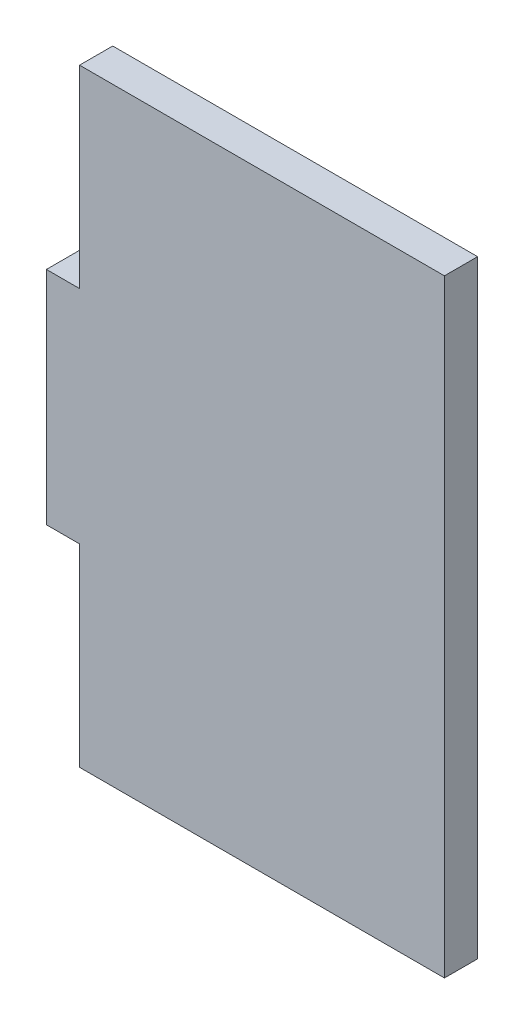
SolidWorks part; units mm, degrees
ref_plane "Alzado" through (0, 0, 0) normal (0, 0, 1) x (1, 0, 0)
ref_plane "Planta" through (0, 0, 0) normal (0, 1, 0) x (1, 0, 0)
ref_plane "Vista lateral" through (0, 0, 0) normal (1, 0, 0) x (0, 0, -1)
sketch "Croquis1" plane through (0, 0, 0) normal (0, 0, 1) x (1, 0, 0)
  line L1 (-16.5, 27.5) -> (16.5, 27.5)
  line L2 (-16.5, 27.5) -> (-16.5, -27.5)
  line L3 (-16.5, -27.5) -> (16.5, -27.5)
  line L4 (16.5, 27.5) -> (16.5, -27.5)
  line L5 (-16.5, 27.5) -> (16.5, -27.5) construction
  line L6 (-16.5, -27.5) -> (16.5, 27.5) construction
  point P0 (0, 0)
  dimension "D1" = 33
  dimension "D2" = 55
extrude "Saliente-Extruir1" add sketch "Croquis1" along normal blind 3
sketch "Croquis2" plane through (0, 0, 3) normal (0, 0, 1) x (1, 0, 0)
  line L0 (0, 0) -> (26.6259, 0) construction
  line L1 (-16.5, 27.5) -> (-16.5, -27.5) construction
  line L3 (-16.5, 10) -> (-16.5, -10)
  line L7 (-16.5, -10) -> (-19.5, -10)
  line L8 (-16.5, -10) -> (-16.5, 10)
  line L9 (-16.5, 10) -> (-19.5, 10)
  line L10 (-19.5, -10) -> (-19.5, 10)
  line M8 (-16.5, 27.5) -> (-16.5, -27.5)
  dimension "D1" = 10
  dimension "D2" = 20
  dimension "D4" = 3
extrude "Saliente-Extruir2" add sketch "Croquis2" against normal blind 3 contours L10 L7 L9 M8
